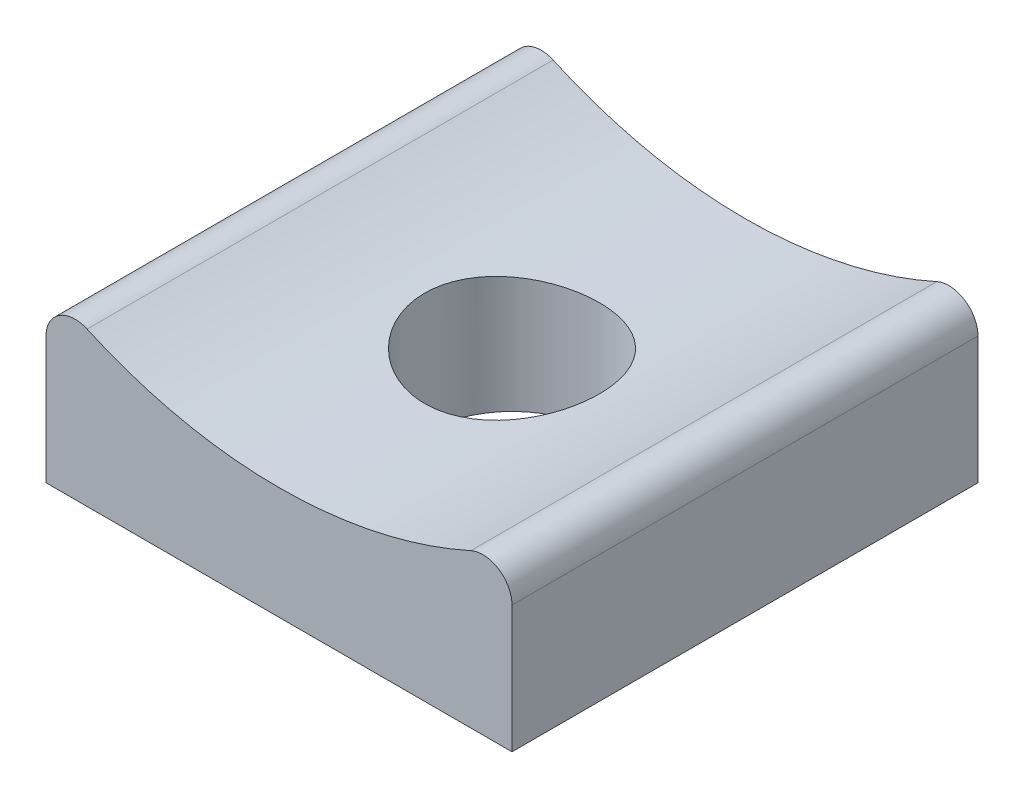
SolidWorks part; units mm, degrees
material "PLA"
ref_plane "Front Plane" through (0, 0, 0) normal (0, 0, 1) x (1, 0, 0)
ref_plane "Top Plane" through (0, 0, 0) normal (0, 1, 0) x (1, 0, 0)
ref_plane "Right Plane" through (0, 0, 0) normal (1, 0, 0) x (0, 0, -1)
sketch "Sketch1" plane through (0, 0, 0) normal (0, 0, 1) x (1, 0, 0)
  line L1 (-4, -9.9282) -> (4, -9.9282)
  line L2 (-4, -9.9282) -> (-4, -6.9282)
  line L3 (-4, -6.9282) -> (4, -6.9282)
  line L4 (4, -9.9282) -> (4, -6.9282)
  line L5 (-4, -9.9282) -> (4, -6.9282) construction
  line L6 (-4, -6.9282) -> (4, -9.9282) construction
  circle A0 centre (0, 0) radius 8
  point P7 (0, -8.4282)
  dimension "D1" = 16
  dimension "D2" = 8
  dimension "D3" = 3
extrude "Boss-Extrude1" add sketch "Sketch1" along normal blind 8 contours A0 L2 L1 L4
fillet "Fillet1" radius 0.5 2 edges at (-4, -6.9282, 4) (4, -6.9282, 4)
sketch "Sketch2" plane through (0, -9.9282, 0) normal (0, -1, 0) x (1, 0, 0)
  line L0 (4, 8) -> (4, 0) construction
  circle A0 centre (0, 4) radius 1.5
  point P4 (4, 4)
  dimension "D1" = 3
extrude "Cut-Extrude1" cut sketch "Sketch2" against normal through all
